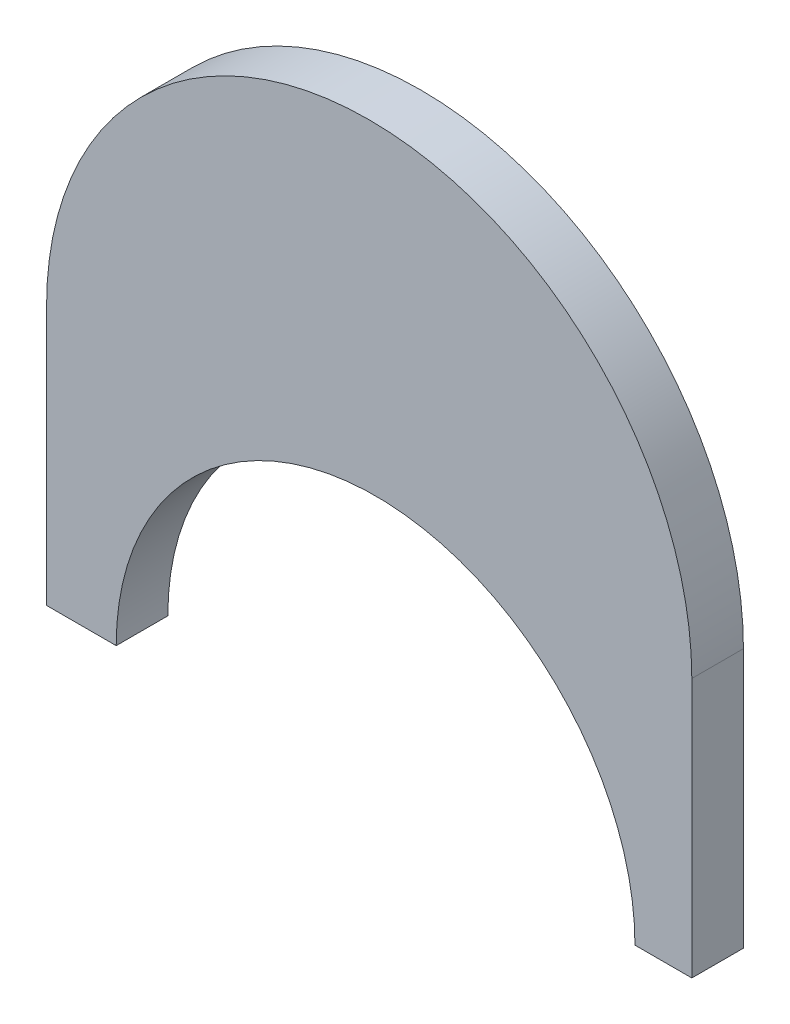
SolidWorks part; units mm, degrees
ref_plane "Front Plane" through (0, 0, 0) normal (0, 0, 1) x (1, 0, 0)
ref_plane "Top Plane" through (0, 0, 0) normal (0, 1, 0) x (1, 0, 0)
ref_plane "Right Plane" through (0, 0, 0) normal (1, 0, 0) x (0, 0, -1)
sketch "Sketch1" plane through (0, 0, 0) normal (0, 0, 1) x (1, 0, 0)
  line L0 (-31.75, 0.0078) -> (31.75, 0.0078)
  line L2 (-31.75, 0.0078) -> (-31.75, -25.5192)
  line L3 (-31.75, -25.5192) -> (-24.8973, -25.5192)
  line L4 (31.75, 0.0078) -> (31.75, -25.5192)
  line L5 (31.75, -25.5192) -> (26.1567, -25.5192)
  arc A0 (-31.75, 0.0078) -> (31.75, 0.0078) centre (0, 0) cw
  arc A2 (26.1567, -25.5192) -> (-24.8973, -25.5192) centre (0.6297, -25.5192) ccw
  point P3 (0, 31.75)
  dimension "D4" = 31.75
  dimension "D2" = 51.054
  dimension "D1" = 0
  dimension "D3" = 31.75
extrude "Boss-Extrude1" add sketch "Sketch1" against normal blind 5.08 contours A2 L0 L2 L3 | A2 L5 L4 L0 | A0 L0
